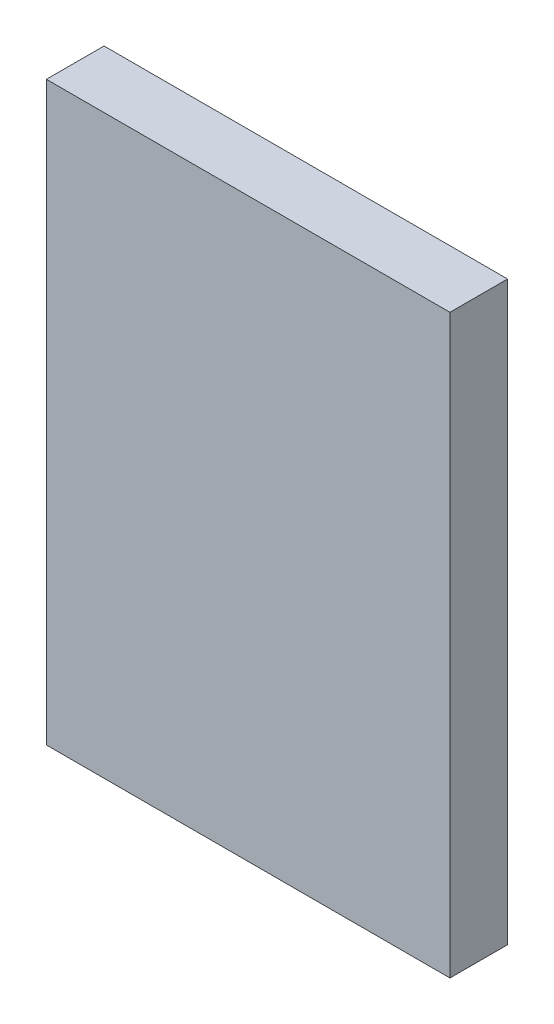
SolidWorks part; units mm, degrees
ref_plane "Front Plane" through (0, 0, 0) normal (0, 0, 1) x (1, 0, 0)
ref_plane "Top Plane" through (0, 0, 0) normal (0, 1, 0) x (1, 0, 0)
ref_plane "Right Plane" through (0, 0, 0) normal (1, 0, 0) x (0, 0, -1)
sketch "Sketch1" plane through (0, 0, 0) normal (0, 0, 1) x (1, 0, 0)
  line L1 (-350, 500) -> (350, 500)
  line L2 (-350, 500) -> (-350, -500)
  line L3 (-350, -500) -> (350, -500)
  line L4 (350, 500) -> (350, -500)
  line L5 (-350, 500) -> (350, -500) construction
  line L6 (-350, -500) -> (350, 500) construction
  point P0 (0, 0)
  dimension "D1" = 1000
  dimension "D2" = 700
extrude "Boss-Extrude1" add sketch "Sketch1" along normal mid plane 100
